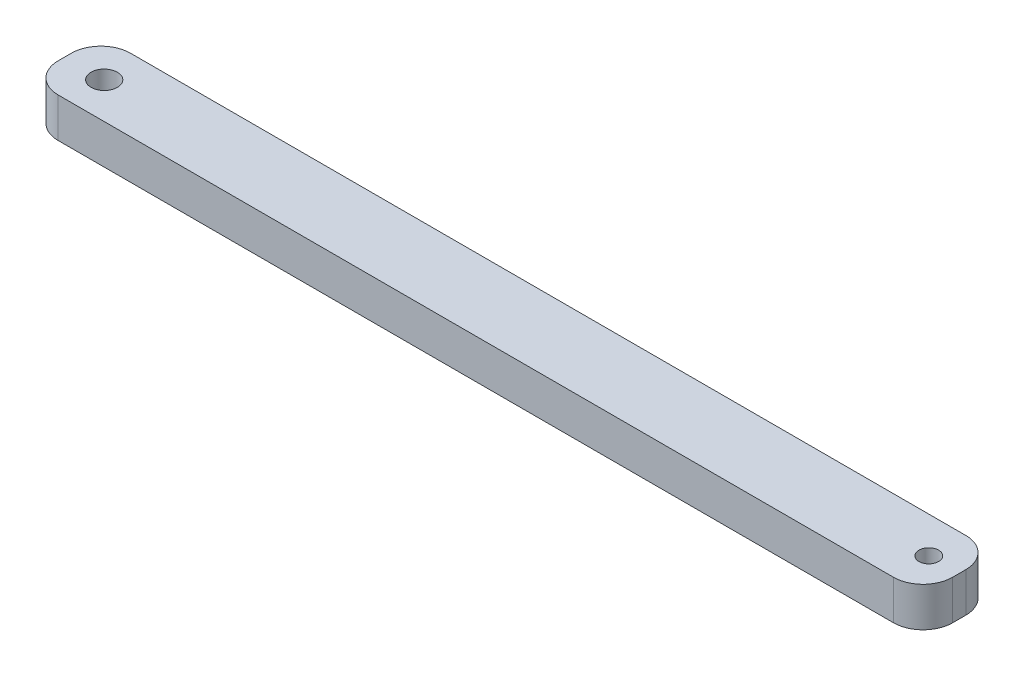
SolidWorks part; units mm, degrees
ref_plane "Alzado" through (0, 0, 0) normal (0, 0, 1) x (1, 0, 0)
ref_plane "Planta" through (0, 0, 0) normal (0, 1, 0) x (1, 0, 0)
ref_plane "Vista lateral" through (0, 0, 0) normal (1, 0, 0) x (0, 0, -1)
sketch "Croquis1" plane through (0, 0, 0) normal (0, 1, 0) x (1, 0, 0)
  line L0 (-29.6369, 10.9405) -> (38.3631, 10.9405) construction
  line L1 (-29.6369, 13.6905) -> (38.3631, 13.6905)
  line L2 (-29.6369, 13.6905) -> (-29.6369, 8.1905)
  line L3 (-29.6369, 8.1905) -> (38.3631, 8.1905)
  line L4 (38.3631, 13.6905) -> (38.3631, 8.1905)
  line L5 (36.0481, 13.6905) -> (36.0481, 8.1905) construction
  line L6 (4.3631, 13.6905) -> (4.3631, 8.1905) construction
  circle A0 centre (36.0481, 10.9405) radius 0.75
  circle A1 centre (-26.6369, 10.9405) radius 1
  dimension "D4" = 1.5
  dimension "D5" = 2
  dimension "D1" = 3
  dimension "D2" = 5.5
  dimension "D3" = 31.685
extrude "Saliente-Extruir1" add sketch "Croquis1" along normal blind 3
fillet "Redondeo1" radius 2.25 4 edges at (-29.6369, 1.5, -13.6905) (-29.6369, 1.5, -8.1905) (38.3631, 1.5, -13.6905) (38.3631, 1.5, -8.1905)
